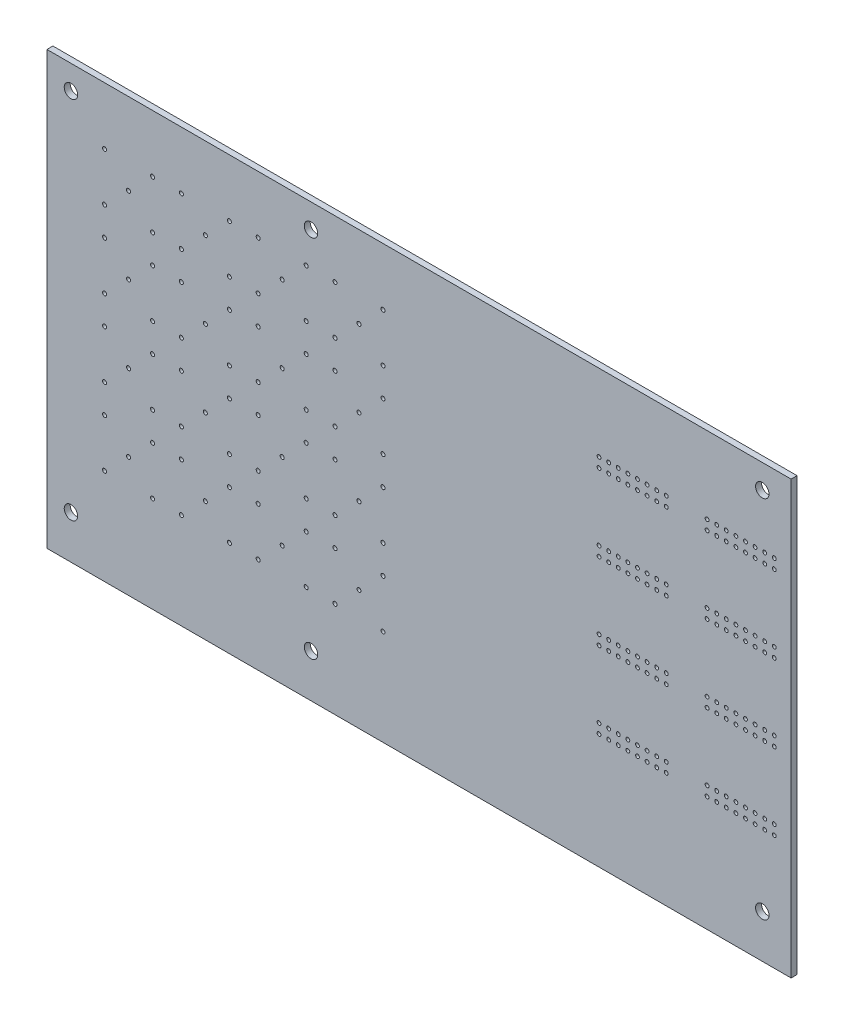
SolidWorks part; units mm, degrees
ref_plane "Front" through (0, 0, 0) normal (0, 0, 1) x (1, 0, 0)
ref_plane "Top" through (0, 0, 0) normal (0, 1, 0) x (1, 0, 0)
ref_plane "Right" through (0, 0, 0) normal (1, 0, 0) x (0, 0, -1)
sketch "Sketch1" plane through (0, 0, 0) normal (0, 0, 1) x (1, 0, 0)
  line L1 (0, 0) -> (196.85, 0)
  line L2 (0, 0) -> (0, -114.3)
  line L3 (0, -114.3) -> (196.85, -114.3)
  line L4 (196.85, 0) -> (196.85, -114.3)
  dimension "D1" = 196.85
  dimension "D2" = 114.3
extrude "PCB outline" add sketch "Sketch1" along normal blind 1.5748
sketch "mounting holes" plane through (0, 0, 1.5748) normal (0, 0, 1) x (1, 0, 0)
  line L0 (0, 0) -> (0, -114.3) construction
  line L1 (196.85, 0) -> (0, 0) construction
  circle A0 centre (6.35, -6.35) radius 1.778
  circle A1 centre (69.85, -6.35) radius 1.778
  circle A2 centre (189.23, -6.35) radius 1.778
  circle A3 centre (189.23, -102.87) radius 1.778
  circle A4 centre (69.85, -102.87) radius 1.778
  circle A5 centre (6.35, -102.87) radius 1.778
  dimension "D1" = 3.556
  dimension "D4" = 3.556
  dimension "D7" = 3.556
  dimension "D8" = 3.556
  dimension "D5" = 3.556
  dimension "D6" = 3.556
  dimension "D2" = 6.35
  dimension "D3" = 6.35
  dimension "D9" = 96.52
  dimension "D10" = 63.5
  dimension "D11" = 119.38
extrude "mounting holes cut" cut sketch "mounting holes" against normal blind 2.54
sketch "Sketch2" plane through (0, 0, 1.5748) normal (0, 0, 1) x (1, 0, 0)
  circle A0 centre (21.59, -21.59) radius 0.5334
  circle A1 centre (27.94, -15.19) radius 0.5334
  circle A2 centre (15.24, -15.19) radius 0.5334
  circle A3 centre (27.94, -27.94) radius 0.5334
  circle A4 centre (15.24, -27.94) radius 0.5334
  circle A5 centre (6.35, -6.35) radius 1.778 construction
  circle A6 centre (6.35, -6.35) radius 1.778 construction
  dimension "D1" = 1.0668
  dimension "D2" = 1.0668
  dimension "D3" = 1.0668
  dimension "D4" = 1.0668
  dimension "D5" = 1.0668
  dimension "D6" = 6.35
  dimension "D7" = 12.75
  dimension "D8" = 12.7
  dimension "D9" = 6.35
  dimension "D10" = 15.24
  dimension "D11" = 15.24
extrude "Cut-Extrude1" cut sketch "Sketch2" against normal blind 1.5748
pattern_linear "LPattern1" count 4 spacing 20.32 along (1, 0, 0) count 4 spacing 20.32 along (0, -1, 0) of "Cut-Extrude1"
sketch "Sketch3" plane through (0, 0, 1.5748) normal (0, 0, 1) x (1, 0, 0)
  line L0 (146.05, -20.32) -> (148.59, -20.32) construction
  line L1 (146.05, -20.32) -> (146.05, -22.86) construction
  circle A0 centre (146.05, -20.32) radius 0.508
  circle A1 centre (148.59, -20.32) radius 0.508
  circle A2 centre (151.13, -20.32) radius 0.508
  circle A3 centre (153.67, -20.32) radius 0.508
  circle A4 centre (156.21, -20.32) radius 0.508
  circle A5 centre (158.75, -20.32) radius 0.508
  circle A6 centre (161.29, -20.32) radius 0.508
  circle A7 centre (163.83, -20.32) radius 0.508
  circle A8 centre (146.05, -22.86) radius 0.508
  circle A9 centre (148.59, -22.86) radius 0.508
  circle A10 centre (151.13, -22.86) radius 0.508
  circle A11 centre (153.67, -22.86) radius 0.508
  circle A12 centre (156.21, -22.86) radius 0.508
  circle A13 centre (158.75, -22.86) radius 0.508
  circle A14 centre (161.29, -22.86) radius 0.508
  circle A15 centre (163.83, -22.86) radius 0.508
  circle A16 centre (82.55, -21.59) radius 0.5334 construction
  dimension "D1" = 1.016
  dimension "D4" = 63.5
  dimension "D3" = 1.27
  dimension "D5" = 2.54
extrude "DIO seed" cut sketch "Sketch3" against normal blind 1.5748
pattern_linear "DIO pattern" count 2 spacing 28.575 along (1, 0, 0) count 4 spacing 20.32 along (0, -1, 0) of "DIO seed"
